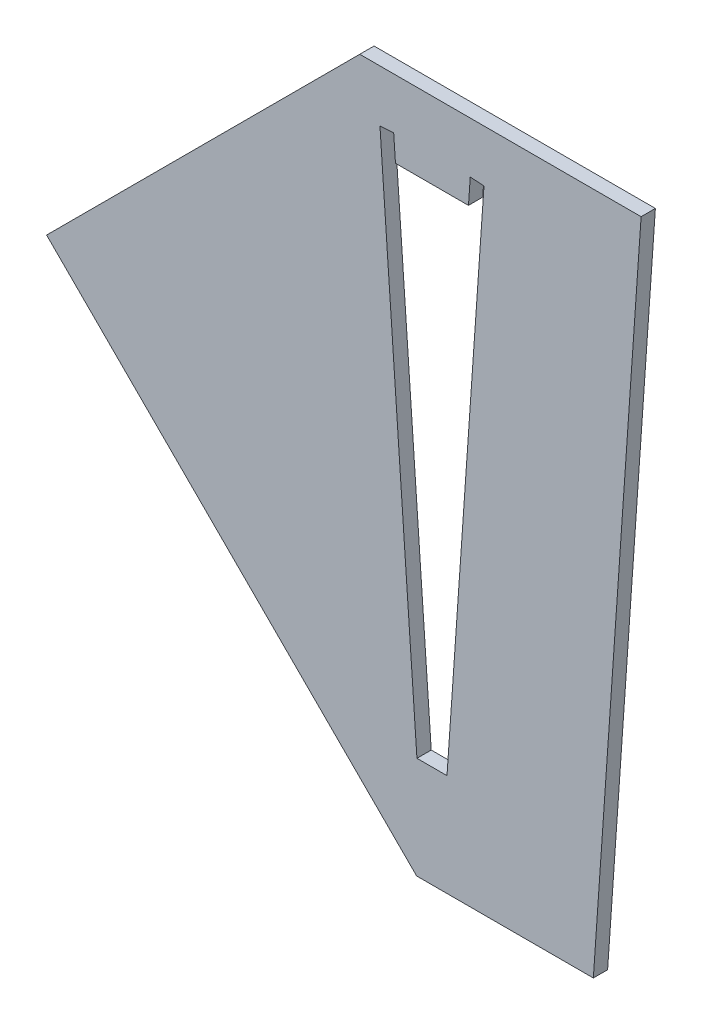
SolidWorks part; units mm, degrees
ref_plane "Front" through (0, 0, 0) normal (0, 0, 1) x (1, 0, 0)
ref_plane "Top" through (0, 0, 0) normal (0, 1, 0) x (1, 0, 0)
ref_plane "Right" through (0, 0, 0) normal (1, 0, 0) x (0, 0, -1)
sketch "Sketch1" plane through (0, 0, 0) normal (0, 0, 1) x (1, 0, 0)
  line L0 (-0.3066, 0) -> (-7.5, 102.8707) construction
  line L1 (-0.3066, 0) -> (-3, -0.1883) construction
  line L2 (-7.5, 102.8707) -> (-10.1934, 102.6824) construction
  line L3 (-3, -0.1883) -> (-10.1934, 102.6824) construction
  line L4 (0.3066, 0) -> (7.5, 102.8707) construction
  line L5 (0.3066, 0) -> (3, -0.1883) construction
  line L6 (7.5, 102.8707) -> (10.1934, 102.6824) construction
  line L7 (3, -0.1883) -> (10.1934, 102.6824) construction
  line L8 (-0.3066, 0) -> (0, 0) construction
  line L9 (0, 0) -> (0.3066, 0) construction
  line L10 (-7.5, 102.8707) -> (7.5, 102.8707) construction
  line L11 (40.9791, 112.8707) -> (-14.1472, 112.8707)
  line L12 (-75.509, 51.509) -> (-3, -21)
  line L13 (-3, -21) -> (31.618, -21)
  line L14 (40.9791, 112.8707) -> (31.618, -21)
  line L15 (0, 0) -> (0, 102.8707) construction
  line L16 (-2.9432, -1) -> (2.9432, -1)
  line L17 (-7.1504, 97.8707) -> (-7.5, 102.8707)
  line L18 (-7.5, 102.8707) -> (-10.1934, 102.6824)
  line L19 (-10.1934, 102.6824) -> (-2.9432, -1)
  line L20 (-7.1504, 97.8707) -> (7.1504, 97.8707)
  line L21 (7.1504, 97.8707) -> (7.5, 102.8707)
  line L22 (7.5, 102.8707) -> (10.1934, 102.6824)
  line L23 (10.1934, 102.6824) -> (2.9432, -1)
  line L24 (-75.509, 51.509) -> (-14.1472, 112.8707)
  point P0 (0, 102.8707)
  dimension "D1" = 2.7
  dimension "D2" = 8
  dimension "D3" = 6
  dimension "D4" = 15
  dimension "D5" = 135
  dimension "D6" = 5
  dimension "D7" = 1
  dimension "D8" = 10
  dimension "D9" = 30
  dimension "D10" = 20
  dimension "D11" = 10
extrude "Boss-Extrude1" add sketch "Sketch1" along normal blind 2.8
